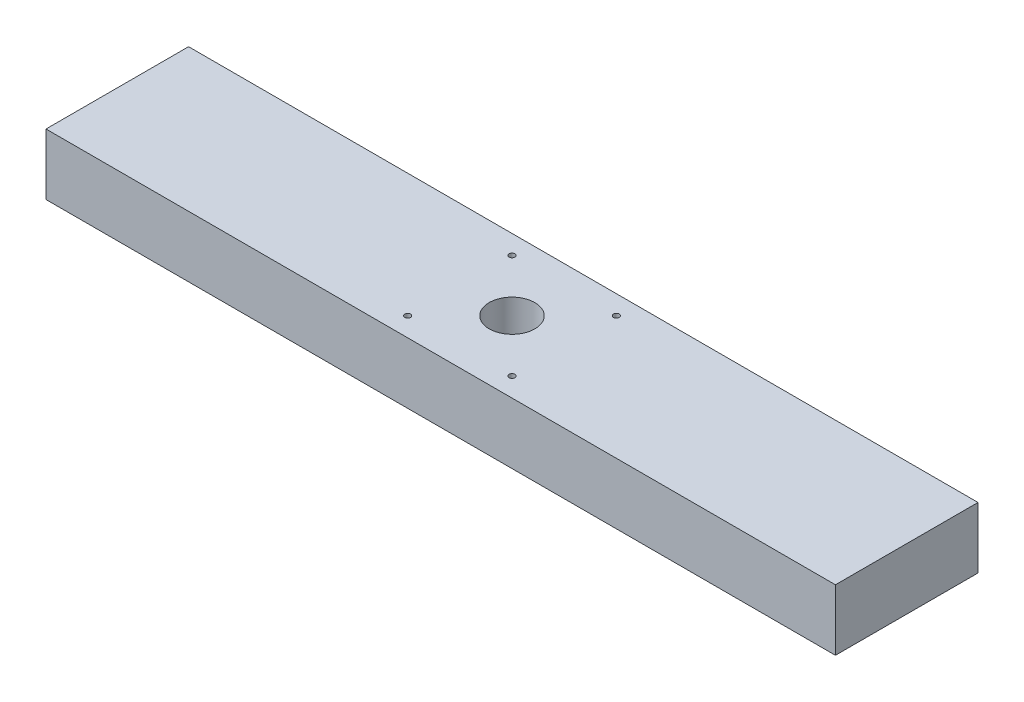
SolidWorks part; units mm, degrees
ref_plane "Front" through (0, 0, 0) normal (0, 0, 1) x (1, 0, 0)
ref_plane "Top" through (0, 0, 0) normal (0, 1, 0) x (1, 0, 0)
ref_plane "Right" through (0, 0, 0) normal (1, 0, 0) x (0, 0, -1)
sketch "Sketch1" plane through (0, 0, 0) normal (0, 1, 0) x (1, 0, 0)
  line L1 (246.126, -44.45) -> (-246.126, -44.45)
  line L2 (246.126, -44.45) -> (246.126, 44.45)
  line L3 (246.126, 44.45) -> (-246.126, 44.45)
  line L4 (-246.126, -44.45) -> (-246.126, 44.45)
  line L5 (246.126, -44.45) -> (-246.126, 44.45) construction
  line L6 (246.126, 44.45) -> (-246.126, -44.45) construction
  point P0 (0, 0)
  dimension "D1" = 492.252
  dimension "D2" = 88.9
extrude "Boss-Extrude1" add sketch "Sketch1" along normal blind 38.1
sketch "Sketch2" plane through (0, 38.1, 0) normal (0, 1, 0) x (1, 0, 0)
  line L5 (32.5501, -32.5501) -> (-32.5501, 32.5501) construction
  line L6 (32.5501, 32.5501) -> (-32.5501, -32.5501) construction
  circle A0 centre (-32.5501, 32.5501) radius 1.8288
  circle A1 centre (-32.5501, -32.5501) radius 1.8288
  circle A2 centre (32.5501, -32.5501) radius 1.8288
  circle A3 centre (32.5501, 32.5501) radius 1.8288
  circle A4 centre (0, 0) radius 14.224
  point P0 (0, 0)
  dimension "D3" = 3.6576
  dimension "D4" = 3.6576
  dimension "D5" = 3.6576
  dimension "D6" = 3.6576
  dimension "D7" = 28.448
  dimension "D1" = 65.1002
  dimension "D2" = 65.1002
extrude "Cut-Extrude1" cut sketch "Sketch2" against normal through all
